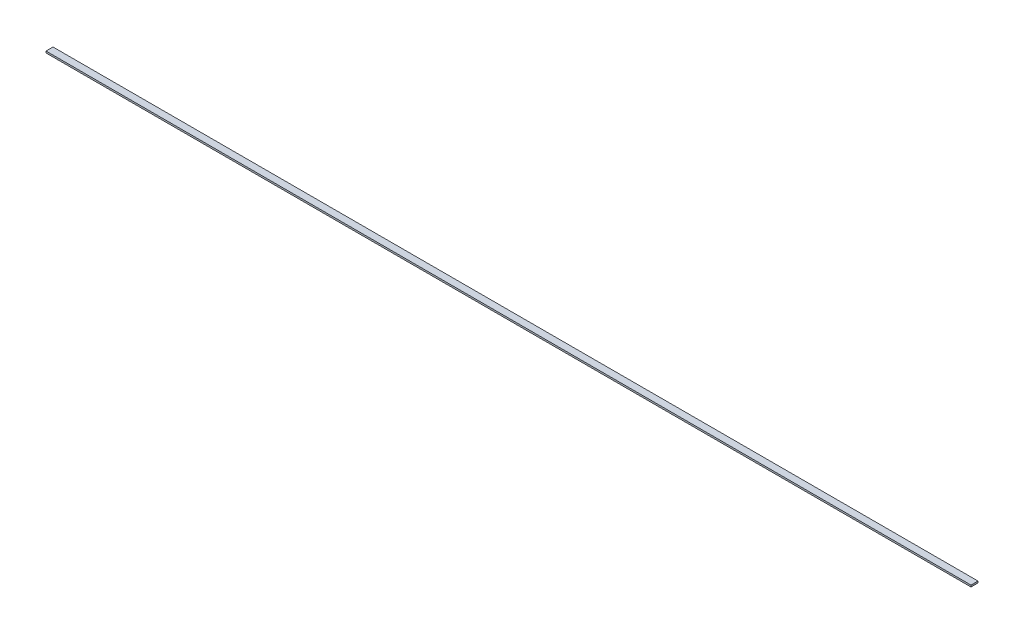
SolidWorks part; units mm, degrees
ref_plane "Спереди" through (0, 0, 0) normal (0, 0, 1) x (1, 0, 0)
ref_plane "Сверху" through (0, 0, 0) normal (0, 1, 0) x (1, 0, 0)
ref_plane "Справа" through (0, 0, 0) normal (1, 0, 0) x (0, 0, -1)
ref_plane "Плоскость4" through (0, -0.545, 0) normal (0, -1, 0) x (1, 0, 0)
sketch "Эскиз1" plane through (0, -0.545, 0) normal (0, -1, 0) x (1, 0, 0)
  line L0 (-298.6129, 0) -> (293.3871, 0)
  line L1 (293.3871, 0) -> (293.3871, 4.4792)
  line L2 (293.3871, 4.4792) -> (-298.6129, 4.4792)
  line L3 (-298.6129, 4.4792) -> (-298.6129, 0)
  dimension "D1" = 592
extrude "Бобышка-Вытянуть1" add sketch "Эскиз1" against normal blind 1.09
